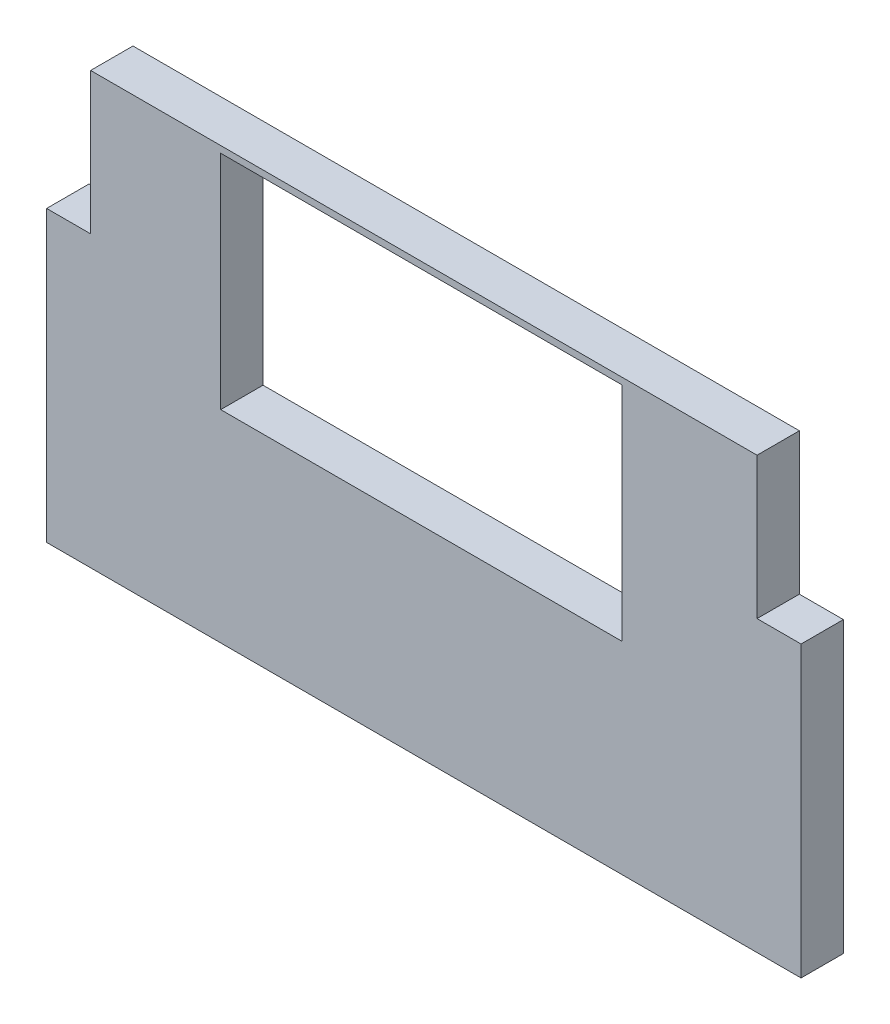
SolidWorks part; units mm, degrees
ref_plane "Front Plane" through (0, 0, 0) normal (0, 0, 1) x (1, 0, 0)
ref_plane "Top Plane" through (0, 0, 0) normal (0, 1, 0) x (1, 0, 0)
ref_plane "Right Plane" through (0, 0, 0) normal (1, 0, 0) x (0, 0, -1)
sketch "Sketch1" plane through (0, 0, 0) normal (0, 0, 1) x (1, 0, 0)
  line L0 (-7.6236, 2.2113) -> (-7.6236, 23.9133)
  line L1 (-7.6236, 23.9133) -> (-4.3216, 23.9133)
  line L2 (-4.3216, 23.9133) -> (-4.3216, 34.5313)
  line L3 (-4.3216, 34.5313) -> (45.6784, 34.5313)
  line L4 (45.6784, 34.5313) -> (45.6784, 23.9133)
  line L5 (45.6784, 23.9133) -> (48.9804, 23.9133)
  line L6 (48.9804, 23.9133) -> (48.9804, 2.2113)
  line L7 (48.9804, 2.2113) -> (-7.6236, 2.2113)
  line L8 (5.4384, 34.0313) -> (35.5384, 34.0313)
  line L9 (5.4384, 34.0313) -> (5.4384, 17.3713)
  line L10 (5.4384, 17.3713) -> (35.5384, 17.3713)
  line L11 (35.5384, 34.0313) -> (35.5384, 17.3713)
extrude "Boss-Extrude1" add sketch "Sketch1" along normal blind 3.175
